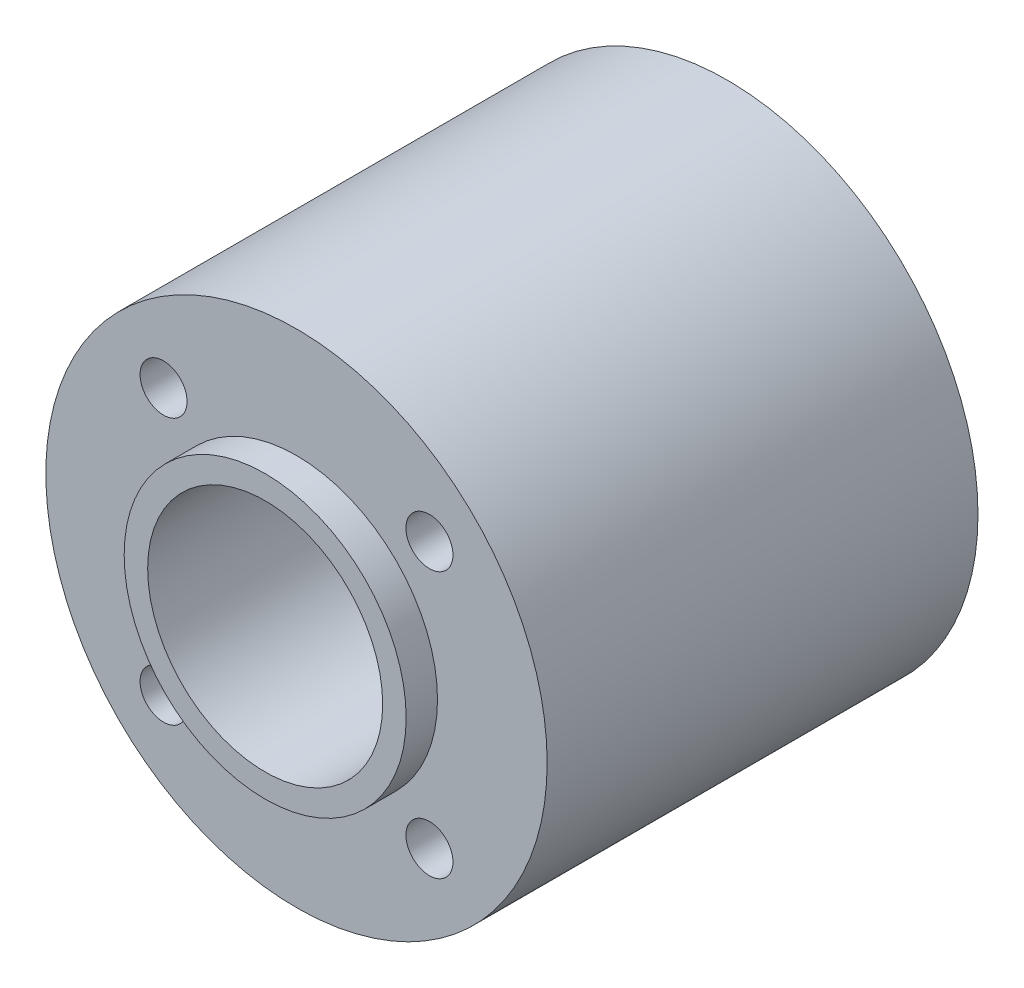
SolidWorks part; units mm, degrees
ref_plane "Front Plane" through (0, 0, 0) normal (0, 0, 1) x (1, 0, 0)
ref_plane "Top Plane" through (0, 0, 0) normal (0, 1, 0) x (1, 0, 0)
ref_plane "Right Plane" through (0, 0, 0) normal (1, 0, 0) x (0, 0, -1)
sketch "Sketch1" plane through (0, 0, 0) normal (0, 0, 1) x (1, 0, 0)
  line L0 (0, 20.8828) -> (0, -21.8655) construction
  line L1 (0, 0) -> (-8.4853, 8.4853) construction
  line L2 (-11.3137, 11.3137) -> (-18.9157, 18.9157) construction
  circle A0 centre (0, 0) radius 16
  circle A1 centre (0, 0) radius 7.5
  circle A2 centre (0, 0) radius 12 construction
  circle A3 centre (-8.4853, 8.4853) radius 1.5
  circle A4 centre (8.4853, 8.4853) radius 1.5
  circle A5 centre (8.4853, -8.4853) radius 1.5
  circle A6 centre (-8.4853, -8.4853) radius 1.5
  point P20 (0, 0)
  dimension "D1" = 32
  dimension "D2" = 15
  dimension "D3" = 24
  dimension "D5" = 3
  dimension "D4" = 45
  dimension "D6" = 4
extrude "Boss-Extrude1" add sketch "Sketch1" along normal blind 27.5
sketch "Sketch2" plane through (0, 0, 27.5) normal (0, 0, 1) x (1, 0, 0)
  circle A0 centre (0, 0) radius 7.5 construction
  circle A1 centre (0, 0) radius 7.5
  circle A2 centre (0, 0) radius 9
  dimension "D1" = 18
extrude "Boss-Extrude2" add sketch "Sketch2" along normal blind 2 and the other way blind 29.5
scale "Scale1" bodies to scale 102 scale about centroid uniform scaling yes scale factor 2
